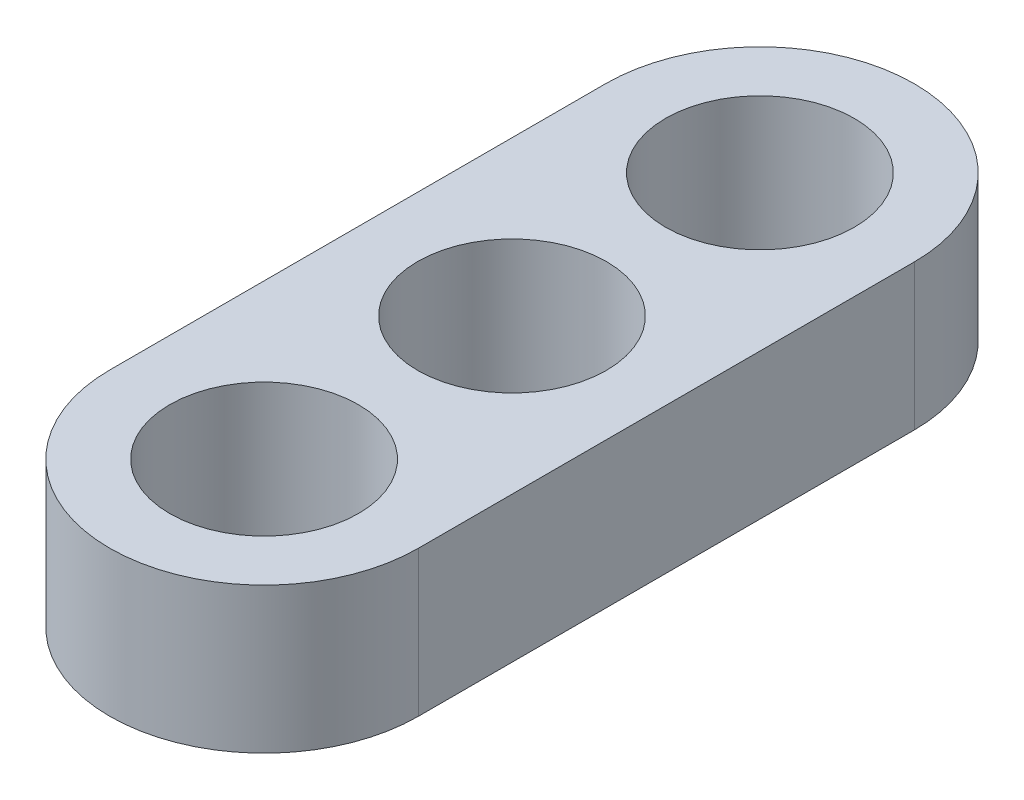
SolidWorks part; units mm, degrees
ref_plane "Front Plane" through (0, 0, 0) normal (0, 0, 1) x (1, 0, 0)
ref_plane "Top Plane" through (0, 0, 0) normal (0, 1, 0) x (1, 0, 0)
ref_plane "Right Plane" through (0, 0, 0) normal (1, 0, 0) x (0, 0, -1)
sketch "Sketch1" plane through (0, 0, 0) normal (0, 1, 0) x (1, 0, 0)
  line L0 (0, -3.937) -> (0, 3.937) construction
  line L1 (-2.4511, -3.937) -> (-2.4511, 3.937)
  line L2 (2.4511, -3.937) -> (2.4511, 3.937)
  arc A0 (-2.4511, -3.937) -> (2.4511, -3.937) centre (0, -3.937) ccw
  arc A1 (2.4511, 3.937) -> (-2.4511, 3.937) centre (0, 3.937) ccw
  circle A2 centre (0, 3.937) radius 1.4986
  circle A3 centre (0, -3.937) radius 1.4986
  circle A4 centre (0, 0) radius 1.4986
  point P2 (0, 0)
  dimension "D2" = 2.9972
  dimension "D1" = 3.937
  dimension "D3" = 4.9022
extrude "Boss-Extrude1" add sketch "Sketch1" along normal blind 2.3114
